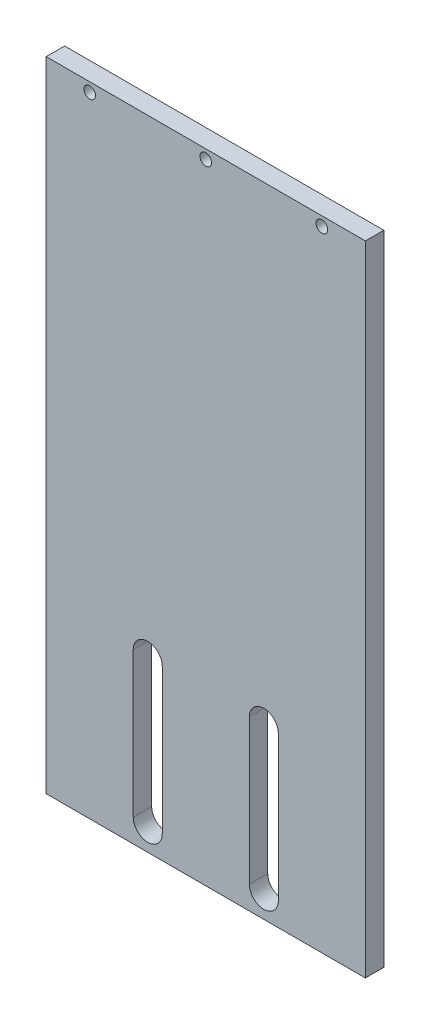
SolidWorks part; units mm, degrees
ref_plane "Alzado" through (0, 0, 0) normal (0, 0, 1) x (1, 0, 0)
ref_plane "Planta" through (0, 0, 0) normal (0, 1, 0) x (1, 0, 0)
ref_plane "Vista lateral" through (0, 0, 0) normal (1, 0, 0) x (0, 0, -1)
sketch "Croquis1" plane through (0, 0, 0) normal (0, 0, 1) x (1, 0, 0)
  line L1 (-55, -110) -> (55, -110)
  line L2 (-55, -110) -> (-55, 110)
  line L3 (-55, 110) -> (55, 110)
  line L4 (55, -110) -> (55, 110)
  line L5 (-55, -110) -> (55, 110) construction
  line L6 (-55, 110) -> (55, -110) construction
  point P0 (0, 0)
  dimension "D1" = 110
  dimension "D2" = 220
extrude "Saliente-Extruir1" add sketch "Croquis1" along normal blind 6.35
sketch "Croquis2" plane through (0, 0, 0) normal (0, 0, 1) x (1, 0, 0)
  line L0 (66.7052, 106.825) -> (-75.6472, 106.825) construction
  line L1 (55, 110) -> (-55, 110) construction
  line L2 (55, -110) -> (55, 110) construction
  line L4 (-55, -110) -> (55, -110) construction
  line L5 (-25, -52) -> (-25, -102)
  line L7 (-15, -102) -> (-15, -52)
  line L8 (15, -52) -> (15, -102)
  line L9 (0, -110) -> (0, -44.8718) construction
  line L10 (25, -102) -> (25, -52)
  circle A0 centre (40, 106.825) radius 2
  circle A1 centre (-40, 106.825) radius 2
  circle A2 centre (0, 106.825) radius 2
  arc A3 (-25, -102) -> (-15, -102) centre (-20, -102) ccw
  arc A8 (15, -102) -> (25, -102) centre (20, -102) ccw
  arc A9 (-15, -52) -> (-25, -52) centre (-20, -52) ccw
  arc A10 (25, -52) -> (15, -52) centre (20, -52) ccw
  dimension "D2" = 4
  dimension "D3" = 4
  dimension "D12" = 50
  dimension "D13" = 50
  dimension "D14" = 4
  dimension "D18" = 10
  dimension "D19" = 10
  dimension "D20" = 10
  dimension "D1" = 3.175
  dimension "D4" = 80
  dimension "D5" = 15
  dimension "D7" = 8
  dimension "D8" = 8
  dimension "D15" = 20
  dimension "D16" = 20
extrude "Cortar-Extruir2" cut sketch "Croquis2" along normal through all
